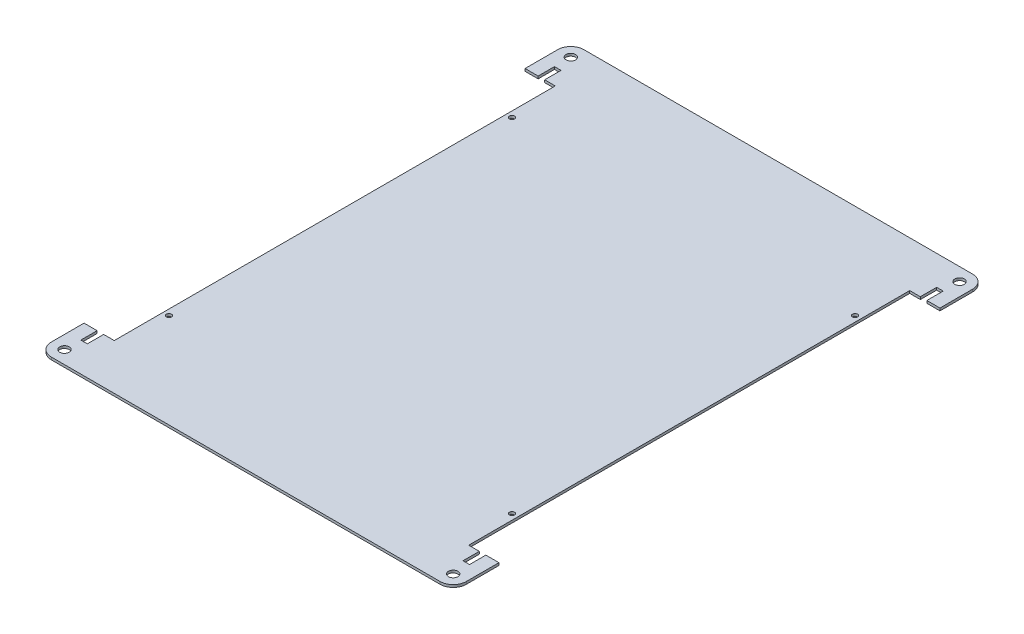
SolidWorks part; units mm, degrees
material "5052-H32"
ref_plane "Front Plane" through (0, 0, 0) normal (0, 0, 1) x (1, 0, 0)
ref_plane "Top Plane" through (0, 0, 0) normal (0, 1, 0) x (1, 0, 0)
ref_plane "Right Plane" through (0, 0, 0) normal (1, 0, 0) x (0, 0, -1)
sketch "Sketch1" plane through (0, 0, 0) normal (0, 1, 0) x (1, 0, 0)
  line L1 (127, 163) -> (-127, 163)
  line L2 (127, 163) -> (127, -163)
  line L3 (127, -163) -> (-127, -163)
  line L4 (-127, 163) -> (-127, -163)
  line L5 (0, -163) -> (0, 163) construction
  line L6 (127, 0) -> (-127, 0) construction
  point P0 (0, 0)
  dimension "D1" = 254
  dimension "D2" = 326
extrude "Boss-Extrude1" add sketch "Sketch1" along normal blind 1.5189
sketch "Sketch2" plane through (0, 1.5189, 0) normal (0, 1, 0) x (1, 0, 0)
  line L1 (105, 105) -> (-105, 105) construction
  line L2 (105, 105) -> (105, -105) construction
  line L3 (105, -105) -> (-105, -105) construction
  line L4 (-105, 105) -> (-105, -105) construction
  line L5 (0, -105) -> (0, 105) construction
  line L6 (105, 0) -> (-105, 0) construction
  point P4 (-105, 105)
  point P6 (-105, -105)
  point P7 (105, -105)
  point P8 (105, 105)
  dimension "D1" = 210
  dimension "D2" = 210
hole_wizard "M2.5 Clearance Hole1" positions "3DSketch1" profile "Sketch3" hole size "M2.5" standard "ANSI Metric"
sketch3d "3DSketch1"
  point P0 (-105, 1.5189, 105)
  point P3 (-105, 1.5189, -105)
  point P6 (105, 1.5189, -105)
  point P9 (105, 1.5189, 105)
sketch "Sketch3" plane through (-105, 1.5189, 105) normal (1, 0, 0) x (0, 0, 1)
  line L0 (0, 0) -> (0, 12.8693)
  line L1 (0, 12.8693) -> (1.55, 11.938)
  line L2 (1.55, 11.938) -> (1.55, 0)
  line L5 (1.55, 0) -> (0, 0)
  line L10 (0, 12.8693) -> (-1.55, 11.938) construction
  line L11 (0, -6.35) -> (0, 107.95) construction
  dimension "Hole Dia." = 3.1
  dimension "Hole Depth" = 11.938
  dimension "Drill Angle" = 118
hole_wizard "M5 Clearance Hole1" positions "Sketch5" profile "Sketch4" hole size "M5" standard "ANSI Metric"
sketch "Sketch5" plane through (0, 1.5189, 0) normal (0, 1, 0) x (1, 0, 0)
  line L0 (-119, 155) -> (119, -155) construction
  point P0 (-119, 155)
  point P2 (119, 155)
  point P4 (119, -155)
  point P6 (-119, -155)
  dimension "D1" = 238
  dimension "D2" = 310
sketch "Sketch4" plane through (-119, 1.5189, -155) normal (1, 0, 0) x (0, 0, 1)
  line L0 (0, 0) -> (0, 13.6805)
  line L1 (0, 13.6805) -> (2.9, 11.938)
  line L2 (2.9, 11.938) -> (2.9, 0)
  line L5 (2.9, 0) -> (0, 0)
  line L10 (0, 13.6805) -> (-2.9, 11.938) construction
  line L11 (0, -6.35) -> (0, 107.95) construction
  dimension "Hole Dia." = 5.8
  dimension "Hole Depth" = 11.938
  dimension "Drill Angle" = 118
fillet "Fillet1" radius 8 4 edges at (127, 0.7595, -163) (-127, 0.7595, -163) (-127, 0.7595, 163) (127, 0.7595, 163)
sketch "Sketch6" plane through (0, 1.5189, 0) normal (0, 1, 0) x (1, 0, 0)
  line L0 (0, 0) -> (0, -50000) construction
  line L1 (127, -155) -> (127, 155) construction
  line L2 (127, 135) -> (108.5, 135)
  line L3 (127, 135) -> (127, -135)
  line L4 (127, -135) -> (108.5, -135)
  line L5 (108.5, 135) -> (108.5, -135)
  line L6 (117, -135) -> (117, 135) construction
  line L7 (127, 0) -> (108.5, 0) construction
  line L8 (115, -140) -> (119, -140) construction
  line L9 (115, 135) -> (119, 135)
  line L10 (115, 135) -> (115, 145)
  line L11 (115, 145) -> (119, 145)
  line L12 (119, 135) -> (119, 145)
  line L13 (117, 145) -> (117, 135) construction
  line L14 (115, 140) -> (119, 140) construction
  line L15 (117, -145) -> (117, -135) construction
  line L16 (119, -135) -> (119, -145)
  line L17 (115, -145) -> (119, -145)
  line L18 (115, -135) -> (115, -145)
  line L19 (115, -135) -> (119, -135)
  line L20 (-117, -145) -> (-117, -135) construction
  line L21 (-115, 140) -> (-119, 140) construction
  line L22 (-117, 145) -> (-117, 135) construction
  line L23 (-115, -140) -> (-119, -140) construction
  line L24 (-127, 0) -> (-108.5, 0) construction
  line L25 (-117, -135) -> (-117, 135) construction
  line L26 (-115, -135) -> (-119, -135)
  line L27 (-115, -135) -> (-115, -145)
  line L28 (-115, -145) -> (-119, -145)
  line L29 (-119, -135) -> (-119, -145)
  line L30 (-119, 135) -> (-119, 145)
  line L31 (-115, 145) -> (-119, 145)
  line L32 (-115, 135) -> (-115, 145)
  line L33 (-115, 135) -> (-119, 135)
  line L34 (-108.5, 135) -> (-108.5, -135)
  line L35 (-127, -135) -> (-108.5, -135)
  line L36 (-127, 135) -> (-127, -135)
  line L37 (-127, 135) -> (-108.5, 135)
  point P20 (117, -140)
  point P43 (-117, 140)
  point P44 (-117, 0)
  point P45 (-117, -140)
  point P75 (117, 0)
  point P110 (117, 140)
  line M17 (127, -155) -> (127, 155)
  line M21 (-127, 155) -> (-127, -155)
  dimension "D1" = 270
  dimension "D2" = 117
  dimension "D3" = 4
  dimension "D4" = 10
  dimension "D5" = 18.5
extrude "Cut-Extrude1" cut sketch "Sketch6" against normal blind 10 contours L2 L5 L4 M17 | L4 L18 L17 L16 | L2 L12 L11 L10 | L37 L35 L26 L34 L33 M21 | L26 L29 L28 L27 | L33 L32 L31 L30
sketch "Sketch7" plane through (0, 1.5189, 0) normal (0, 1, 0) x (1, 0, 0)
  line L0 (0, 0) -> (-50000, 0) construction
  line L1 (-100, 163) -> (0, 113)
  line L2 (119, 163) -> (-119, 163) construction
  line L3 (0, 113) -> (100, 163)
  line L4 (100, 163) -> (-100, 163)
  line L5 (100, -163) -> (-100, -163)
  line L6 (0, -113) -> (100, -163)
  line L7 (-100, -163) -> (0, -113)
  dimension "D1" = 50
  dimension "D2" = 200
extrude "Cut-Extrude2" [suppressed] cut sketch "Sketch7" against normal blind 10
fillet "Fillet2" [suppressed] radius 50
sketch "Sketch8" plane through (0, 1.5189, 0) normal (0, 1, 0) x (1, 0, 0)
  line L1 (50, 50) -> (-50, 50)
  line L2 (50, 50) -> (50, -50)
  line L3 (50, -50) -> (-50, -50)
  line L4 (-50, 50) -> (-50, -50)
  line L5 (0, -50) -> (0, 50) construction
  line L6 (50, 0) -> (-50, 0) construction
  point P0 (0, 0)
  dimension "D1" = 100
  dimension "D2" = 100
extrude "Cut-Extrude3" [suppressed] cut sketch "Sketch8" against normal blind 10
